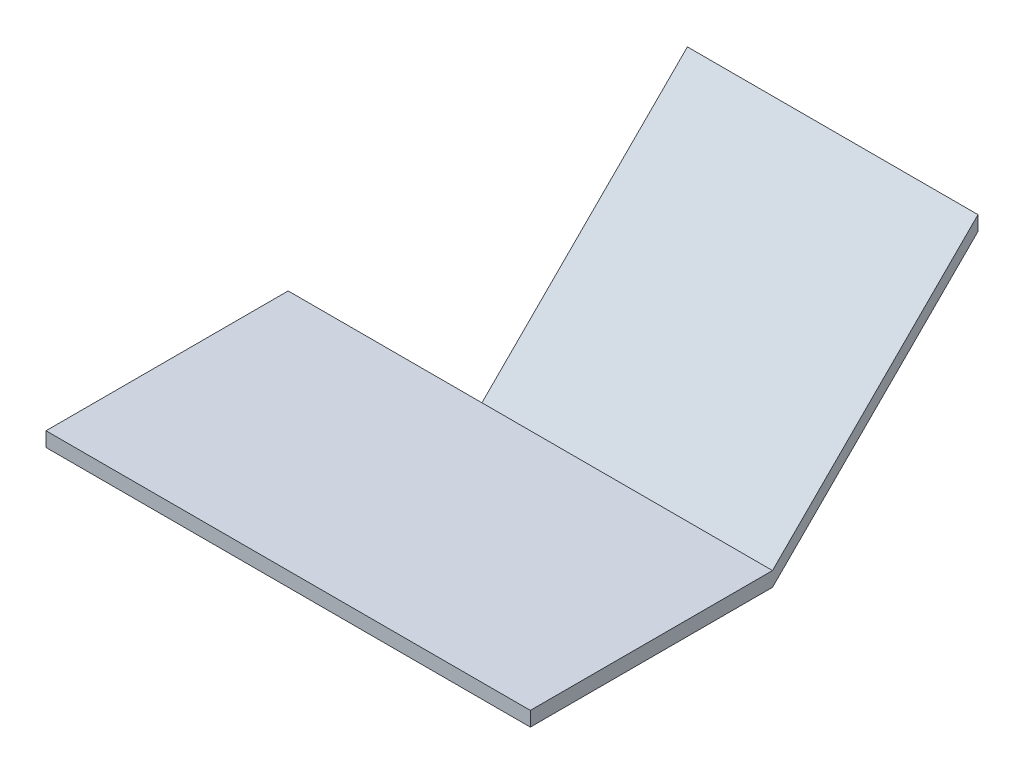
SolidWorks part; units mm, degrees
ref_plane "Front Plane" through (0, 0, 0) normal (0, 0, 1) x (1, 0, 0)
ref_plane "Top Plane" through (0, 0, 0) normal (0, 1, 0) x (1, 0, 0)
ref_plane "Right Plane" through (0, 0, 0) normal (1, 0, 0) x (0, 0, -1)
sketch "Sketch2" plane through (0, 0, 0) normal (0, 1, 0) x (1, 0, 0)
  line L1 (-50, -25) -> (50, -25)
  line L2 (-50, -25) -> (-50, 25)
  line L3 (-50, 25) -> (50, 25)
  line L4 (50, -25) -> (50, 25)
  line L5 (-50, -25) -> (50, 25) construction
  line L6 (-50, 25) -> (50, -25) construction
  point P0 (0, 0)
  dimension "D1" = 100
  dimension "D2" = 50
extrude "Boss-Extrude1" add sketch "Sketch2" against normal blind 3
sketch "Sketch3" plane through (50, 0, 0) normal (1, 0, 0) x (0, 0, -1)
  line L0 (25, 0) -> (67.4264, 42.4264)
  line L1 (67.4264, 42.4264) -> (67.4264, 39.4264)
  line L2 (67.4264, 39.4264) -> (25, -3)
  line L3 (25, -3) -> (25, 0) construction
  line L4 (-25, -3) -> (25, -3) construction
  line L5 (25, -3) -> (25, 0)
  dimension "D1" = 60
  dimension "D2" = 45
extrude "Boss-Extrude2" add sketch "Sketch3" against normal blind 60
equation "\"imageTargetSize\" = 60mm"
equation "\"D1@Sketch3\"=\"imageTargetSize\""
equation "\"D1@Boss-Extrude2\"=\"imageTargetSize\""
equation "\"baseWidth\" = 100mm"
equation "\"D1@Sketch2\"=\"baseWidth\""
equation "\"baseLength\"= 50mm"
equation "\"D2@Sketch2\"=\"baseLength\""
